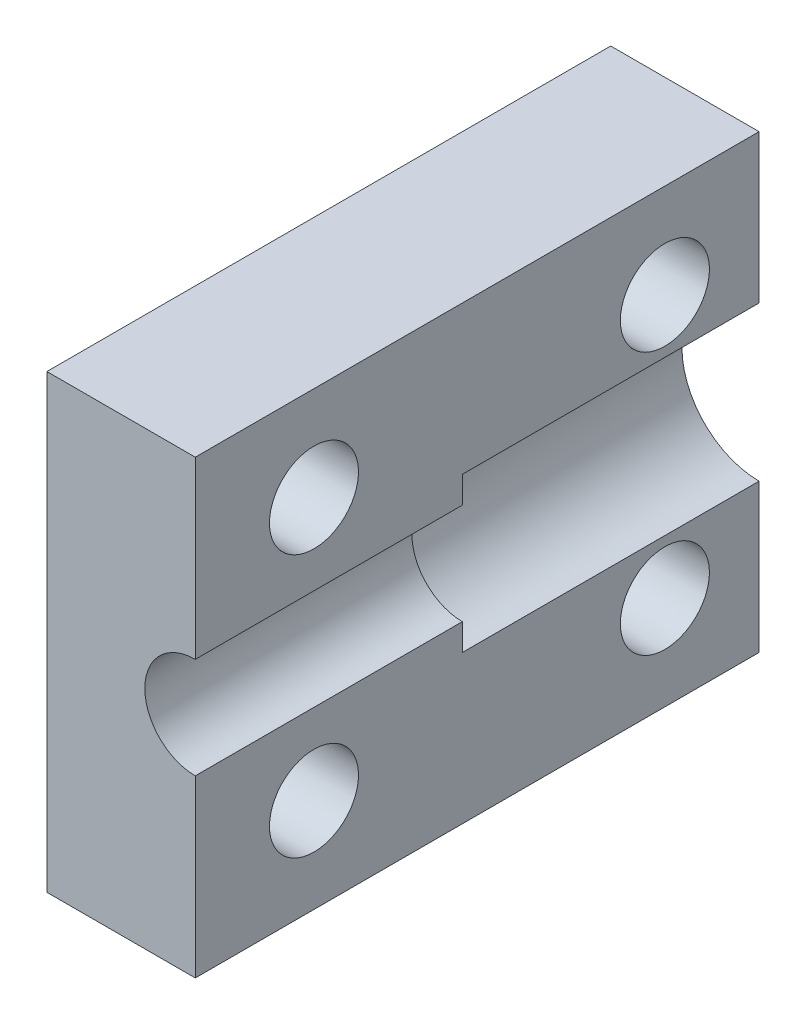
SolidWorks part; units mm, degrees
ref_plane "Front Plane" through (0, 0, 0) normal (0, 0, 1) x (1, 0, 0)
ref_plane "Top Plane" through (0, 0, 0) normal (0, 1, 0) x (1, 0, 0)
ref_plane "Right Plane" through (0, 0, 0) normal (1, 0, 0) x (0, 0, -1)
sketch "Sketch1" plane through (0, 0, 0) normal (0, 0, 1) x (1, 0, 0)
  line L0 (0, 2.6) -> (0, 7.6)
  line L1 (0, 7.6) -> (-5, 7.6)
  line L2 (0, -2.6) -> (0, -7.6)
  line L3 (0, -7.6) -> (-5, -7.6)
  line L4 (-5, -7.6) -> (-5, 7.6)
  circle A0 centre (0, 0) radius 2.6 construction
  arc A1 (0, 2.6) -> (0, -2.6) centre (0, 0) ccw
extrude "Extrude1" add sketch "Sketch1" along normal blind 10
sketch "Sketch2" plane through (0, 0, 10) normal (0, 0, 1) x (1, 0, 0)
  line L0 (0, 1.7) -> (0, 7.6)
  line L1 (0, 7.6) -> (-5, 7.6)
  line L2 (-5, 7.6) -> (-5, -7.6)
  line L3 (-5, 7.6) -> (-5, -7.6) construction
  line L4 (-5, -7.6) -> (0, -7.6)
  line L5 (0, -7.6) -> (0, -1.7)
  circle A0 centre (0, 0) radius 1.7 construction
  arc A1 (0, 1.7) -> (0, -1.7) centre (0, 0) ccw
extrude "Extrude2" add sketch "Sketch2" along normal blind 9
sketch "Sketch4" plane through (-5, 0, 0) normal (-1, 0, 0) x (0, 0, 1)
  line L0 (-1.5875, 4.425) -> (20.6375, 4.425) construction
  line L1 (-1.5875, -4.425) -> (20.6375, -4.425) construction
  line L2 (15, 7.9375) -> (15, -7.9375) construction
  line L3 (3.175, 7.9375) -> (3.175, -7.9375) construction
  line L4 (0, 7.6) -> (0, -7.6) construction
  line L5 (19, 7.6) -> (19, -7.6) construction
  line L6 (19, 7.6) -> (0, 7.6) construction
  line L7 (19, -7.6) -> (0, -7.6) construction
  circle A0 centre (3.175, 4.425) radius 1.5
  circle A1 centre (15, 4.425) radius 1.5
  circle A2 centre (15, -4.425) radius 1.5
  circle A3 centre (3.175, -4.425) radius 1.5
  dimension "D5" = 4.425
  dimension "D1" = 3.175
  dimension "D2" = 4
  dimension "D3" = 3.175
  dimension "D4" = 3.175
extrude "Extrude3" cut sketch "Sketch4" against normal through all
